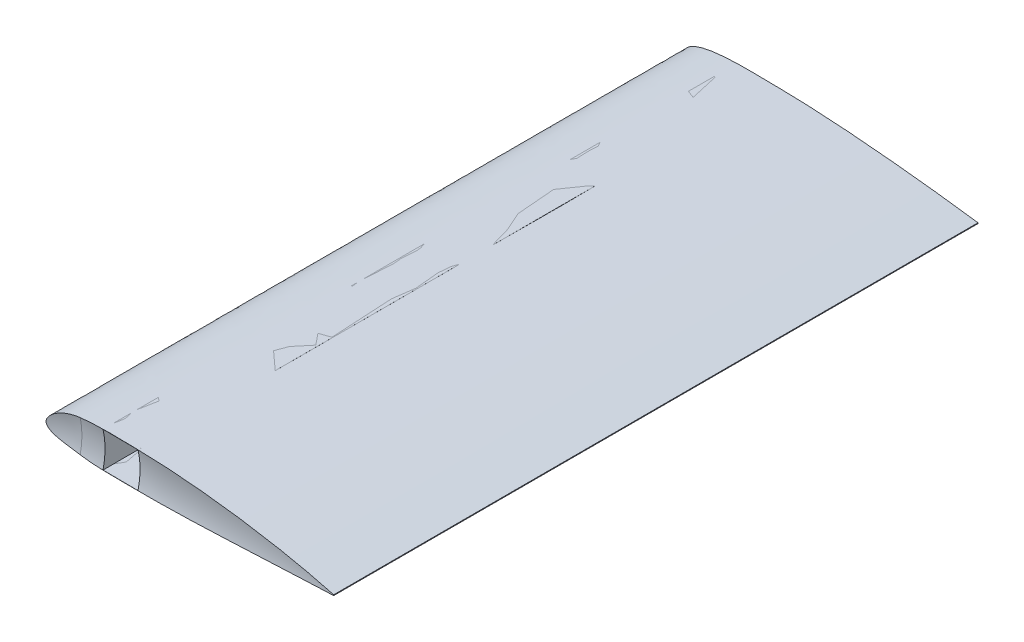
SolidWorks part; units mm, degrees
ref_plane "Front Plane" through (0, 0, 0) normal (0, 0, 1) x (1, 0, 0)
ref_plane "Top Plane" through (0, 0, 0) normal (0, 1, 0) x (1, 0, 0)
ref_plane "Right Plane" through (0, 0, 0) normal (1, 0, 0) x (0, 0, -1)
curve "Curve2"
  spline degree 3 poles (25.4, 0.032, 0) (24.9768, 0.0904, 0) (24.1307, 0.2071, 0) (22.8605, 0.3691, 0) (21.5905, 0.5229, 0) (20.3205, 0.6676, 0) (19.0504, 0.804, 0) (17.7804, 0.9321, 0) (16.5104, 1.0514, 0) (15.2404, 1.1606, 0) (13.9704, 1.2598, 0) (12.692, 1.3473, 0) (11.4135, 1.4221, 0) (10.1349, 1.4776, 0) (8.8649, 1.5185, 0) (7.8146, 1.5178, 0) (6.9766, 1.5373, 0) (6.35, 1.546, 0) (5.715, 1.5506, 0) (5.0799, 1.5478, 0) (4.4448, 1.5346, 0) (3.8095, 1.5078, 0) (3.1738, 1.462, 0) (2.5803, 1.3959, 0) (2.0289, 1.3055, 0) (1.6052, 1.2091, 0) (1.2675, 1.107, 0) (1.012, 1.0136, 0) (0.7549, 0.8965, 0) (0.4933, 0.743, 0) (0.2762, 0.5635, 0) (0.0851, 0.3233, 0) (-0.0556, 0, 0) (0.0851, -0.3233, 0) (0.2762, -0.5635, 0) (0.4933, -0.743, 0) (0.7549, -0.8965, 0) (1.012, -1.0136, 0) (1.2675, -1.107, 0) (1.6052, -1.2091, 0) (2.0289, -1.3055, 0) (2.5803, -1.3959, 0) (3.1738, -1.462, 0) (3.8095, -1.5078, 0) (4.4448, -1.5346, 0) (5.0799, -1.5478, 0) (5.715, -1.5506, 0) (6.35, -1.546, 0) (6.9766, -1.5373, 0) (7.8146, -1.5178, 0) (8.8649, -1.5185, 0) (10.1349, -1.4776, 0) (11.4135, -1.4221, 0) (12.692, -1.3473, 0) (13.9704, -1.2598, 0) (15.2404, -1.1606, 0) (16.5104, -1.0514, 0) (17.7804, -0.9321, 0) (19.0504, -0.804, 0) (20.3205, -0.6676, 0) (21.5905, -0.5229, 0) (22.8605, -0.3691, 0) (24.1307, -0.2071, 0) (24.9768, -0.0904, 0) (25.4, -0.032, 0) knots 0 0 0 0 0.024634 0.049243 0.07383 0.098397 0.122946 0.147479 0.171995 0.196494 0.220976 0.245442 0.27038 0.294813 0.319232 0.343642 0.35536 0.367566 0.379771 0.391975 0.404183 0.416399 0.428636 0.44092 0.450818 0.460843 0.465946 0.471149 0.476523 0.482208 0.488618 0.492568 0.5 0.507432 0.511382 0.517792 0.523477 0.528851 0.534054 0.539157 0.549182 0.55908 0.571364 0.583601 0.595817 0.608025 0.620229 0.632434 0.64464 0.656358 0.680768 0.705187 0.72962 0.754558 0.779024 0.803506 0.828005 0.852521 0.877054 0.901603 0.92617 0.950757 0.975366 1 1 1 1
sketch "Sketch3" plane through (0, 0, 0) normal (0, 0, 1) x (1, 0, 0)
  line L0 (158.75, 0.2) -> (158.75, -0.2)
  spline S1 degree 3 poles (158.75, 0.2) (156.1048, 0.5649) (150.8171, 1.2943) (142.8784, 2.3067) (134.9408, 3.2684) (127.0028, 4.1722) (119.0652, 5.0249) (111.1277, 5.8254) (103.1903, 6.5715) (95.2526, 7.254) (87.3152, 7.8739) (79.3248, 8.4206) (71.3345, 8.8884) (63.3434, 9.2348) (55.4054, 9.4907) (48.8415, 9.4863) (43.6035, 9.6083) (39.6877, 9.6628) (35.7188, 9.6915) (31.7496, 9.6739) (27.7799, 9.5915) (23.8091, 9.4239) (19.8365, 9.1376) (16.1269, 8.7246) (12.6805, 8.1595) (10.0325, 7.5569) (7.9221, 6.9188) (6.3248, 6.335) (4.7181, 5.603) (3.0829, 4.6438) (1.7265, 3.522) (0.5319, 2.0204) (-0.3474, 0) (0.5319, -2.0204) (1.7265, -3.522) (3.0829, -4.6438) (4.7181, -5.603) (6.3248, -6.335) (7.9221, -6.9188) (10.0325, -7.5569) (12.6805, -8.1595) (16.1269, -8.7246) (19.8365, -9.1376) (23.8091, -9.4239) (27.7799, -9.5915) (31.7496, -9.6739) (35.7188, -9.6915) (39.6877, -9.6628) (43.6035, -9.6083) (48.8415, -9.4863) (55.4054, -9.4907) (63.3434, -9.2348) (71.3345, -8.8884) (79.3248, -8.4206) (87.3152, -7.8739) (95.2526, -7.254) (103.1903, -6.5715) (111.1277, -5.8254) (119.0652, -5.0249) (127.0028, -4.1722) (134.9408, -3.2684) (142.8784, -2.3067) (150.8171, -1.2943) (156.1048, -0.5649) (158.75, -0.2) knots 0 0 0 0 0.024634 0.049243 0.07383 0.098397 0.122946 0.147479 0.171995 0.196494 0.220976 0.245442 0.27038 0.294813 0.319232 0.343642 0.35536 0.367566 0.379771 0.391975 0.404183 0.416399 0.428636 0.44092 0.450818 0.460843 0.465946 0.471149 0.476523 0.482208 0.488618 0.492568 0.5 0.507432 0.511382 0.517792 0.523477 0.528851 0.534054 0.539157 0.549182 0.55908 0.571364 0.583601 0.595817 0.608025 0.620229 0.632434 0.64464 0.656358 0.680768 0.705187 0.72962 0.754558 0.779024 0.803506 0.828005 0.852521 0.877054 0.901603 0.92617 0.950757 0.975366 1 1 1 1
ref_plane "Plane1" through (0, 0, 381) normal (0, 0, 1) x (1, 0, 0)
sketch "Sketch4" plane through (0, 0, 381) normal (0, 0, 1) x (1, 0, 0)
  line L0 (158.75, 0.2) -> (158.75, -0.2)
  spline S0 degree 3 poles (830.2199, 1868.0519) (427.3227, -74.4051) (289.079, -16.3388) (142.8784, 2.3067) (134.9408, 3.2684) (127.0028, 4.1722) (119.0652, 5.0249) (111.1277, 5.8254) (103.1903, 6.5715) (95.2526, 7.254) (87.3152, 7.8739) (79.3248, 8.4206) (71.3345, 8.8884) (63.3434, 9.2348) (55.4054, 9.4907) (48.8415, 9.4863) (43.6035, 9.6083) (39.6877, 9.6628) (35.7188, 9.6915) (31.7496, 9.6739) (27.7799, 9.5915) (23.8091, 9.4239) (19.8365, 9.1376) (16.1269, 8.7246) (12.6805, 8.1595) (10.0325, 7.5569) (7.9221, 6.9188) (6.3248, 6.335) (4.7181, 5.603) (3.0829, 4.6438) (1.7265, 3.522) (0.5319, 2.0204) (-0.3474, 0) (0.5319, -2.0204) (1.7265, -3.522) (3.0829, -4.6438) (4.7181, -5.603) (6.3248, -6.335) (7.9221, -6.9188) (10.0325, -7.5569) (12.6805, -8.1595) (16.1269, -8.7246) (19.8365, -9.1376) (23.8091, -9.4239) (27.7799, -9.5915) (31.7496, -9.6739) (35.7188, -9.6915) (39.6877, -9.6628) (43.6035, -9.6083) (48.8415, -9.4863) (55.4054, -9.4907) (63.3434, -9.2348) (71.3345, -8.8884) (79.3248, -8.4206) (87.3152, -7.8739) (95.2526, -7.254) (103.1903, -6.5715) (111.1277, -5.8254) (119.0652, -5.0249) (127.0028, -4.1722) (134.9408, -3.2684) (142.8784, -2.3067) (289.0784, 16.3387) (427.3216, 74.4046) (830.2148, -1868.0272) knots -1.285834 -1.285834 -1.285834 -1.285834 0.024634 0.049243 0.07383 0.098397 0.122946 0.147479 0.171995 0.196494 0.220976 0.245442 0.27038 0.294813 0.319232 0.343642 0.35536 0.367566 0.379771 0.391975 0.404183 0.416399 0.428636 0.44092 0.450818 0.460843 0.465946 0.471149 0.476523 0.482208 0.488618 0.492568 0.5 0.507432 0.511382 0.517792 0.523477 0.528851 0.534054 0.539157 0.549182 0.55908 0.571364 0.583601 0.595817 0.608025 0.620229 0.632434 0.64464 0.656358 0.680768 0.705187 0.72962 0.754558 0.779024 0.803506 0.828005 0.852521 0.877054 0.901603 0.92617 0.950757 0.975366 2.285828 2.285828 2.285828 2.285828 only from (158.75, 0.2) to (158.75, -0.2) construction
  spline S1 degree 3 poles (158.75, 0.2) (156.1048, 0.5649) (150.8171, 1.2943) (142.8784, 2.3067) (134.9408, 3.2684) (127.0028, 4.1722) (119.0652, 5.0249) (111.1277, 5.8254) (103.1903, 6.5715) (95.2526, 7.254) (87.3152, 7.8739) (79.3248, 8.4206) (71.3345, 8.8884) (63.3434, 9.2348) (55.4054, 9.4907) (48.8415, 9.4863) (43.6035, 9.6083) (39.6877, 9.6628) (35.7188, 9.6915) (31.7496, 9.6739) (27.7799, 9.5915) (23.8091, 9.4239) (19.8365, 9.1376) (16.1269, 8.7246) (12.6805, 8.1595) (10.0325, 7.5569) (7.9221, 6.9188) (6.3248, 6.335) (4.7181, 5.603) (3.0829, 4.6438) (1.7265, 3.522) (0.5319, 2.0204) (-0.3474, 0) (0.5319, -2.0204) (1.7265, -3.522) (3.0829, -4.6438) (4.7181, -5.603) (6.3248, -6.335) (7.9221, -6.9188) (10.0325, -7.5569) (12.6805, -8.1595) (16.1269, -8.7246) (19.8365, -9.1376) (23.8091, -9.4239) (27.7799, -9.5915) (31.7496, -9.6739) (35.7188, -9.6915) (39.6877, -9.6628) (43.6035, -9.6083) (48.8415, -9.4863) (55.4054, -9.4907) (63.3434, -9.2348) (71.3345, -8.8884) (79.3248, -8.4206) (87.3152, -7.8739) (95.2526, -7.254) (103.1903, -6.5715) (111.1277, -5.8254) (119.0652, -5.0249) (127.0028, -4.1722) (134.9408, -3.2684) (142.8784, -2.3067) (150.8171, -1.2943) (156.1048, -0.5649) (158.75, -0.2) knots 0 0 0 0 0.024634 0.049243 0.07383 0.098397 0.122946 0.147479 0.171995 0.196494 0.220976 0.245442 0.27038 0.294813 0.319232 0.343642 0.35536 0.367566 0.379771 0.391975 0.404183 0.416399 0.428636 0.44092 0.450818 0.460843 0.465946 0.471149 0.476523 0.482208 0.488618 0.492568 0.5 0.507432 0.511382 0.517792 0.523477 0.528851 0.534054 0.539157 0.549182 0.55908 0.571364 0.583601 0.595817 0.608025 0.620229 0.632434 0.64464 0.656358 0.680768 0.705187 0.72962 0.754558 0.779024 0.803506 0.828005 0.852521 0.877054 0.901603 0.92617 0.950757 0.975366 1 1 1 1
loft "Loft1" add profiles "Sketch3", "Sketch4"
sketch "Sketch5" plane through (0, 0, 0) normal (0, 0, -1) x (-1, 0, 0)
  line L1 (-28.575, 9.525) -> (-47.625, 9.525)
  line L2 (-28.575, 9.525) -> (-28.575, -9.525)
  line L3 (-28.575, -9.525) -> (-47.625, -9.525)
  line L4 (-47.625, 9.525) -> (-47.625, -9.525)
  line L5 (-28.575, 9.525) -> (-47.625, -9.525) construction
  line L6 (-28.575, -9.525) -> (-47.625, 9.525) construction
  point P0 (-38.1, 0)
  point P5 (-50.7921, 0.8957)
  point P7 (0, 0)
  dimension "D1" = 19.05
  dimension "D2" = 38.1
  dimension "D3" = 19.05
extrude "Cut-Extrude1" cut sketch "Sketch5" against normal through all
sketch "Sketch7" plane through (0, 0, 0) normal (0, 1, 0) x (1, 0, 0)
  line L2 (348.869, -382.27) -> (-25.4635, -382.27)
  arc A4 (16.129, -423.8625) -> (348.869, -382.27) centre (27.0529, 840.5023) ccw
  arc A5 (-25.4635, -382.27) -> (16.129, -423.8625) centre (16.129, -382.27) ccw
revolve "Cut-Revolve1" cut sketch "Sketch7" angle 360 about L2
